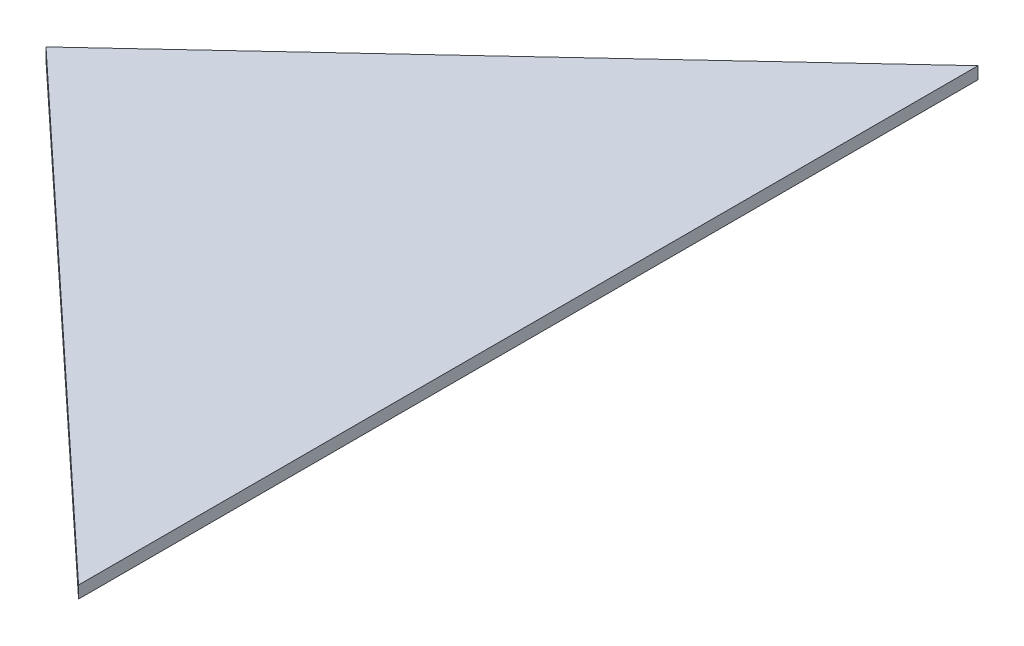
SolidWorks part; units mm, degrees
ref_plane "Front Plane" through (0, 0, 0) normal (0, 0, 1) x (1, 0, 0)
ref_plane "Top Plane" through (0, 0, 0) normal (0, 1, 0) x (1, 0, 0)
ref_plane "Right Plane" through (0, 0, 0) normal (1, 0, 0) x (0, 0, -1)
sketch "Sketch1" plane through (0, 0, 0) normal (0, 1, 0) x (1, 0, 0)
  line L0 (0, 0) -> (125.3906, 116.9286)
  line L1 (125.3906, 116.9286) -> (125.3906, -116.9286)
  line L2 (125.3906, -116.9286) -> (0, 0)
  dimension "D1" = 86
  dimension "D2" = 171.45
extrude "Boss-Extrude1" add sketch "Sketch1" along normal blind 3.175
